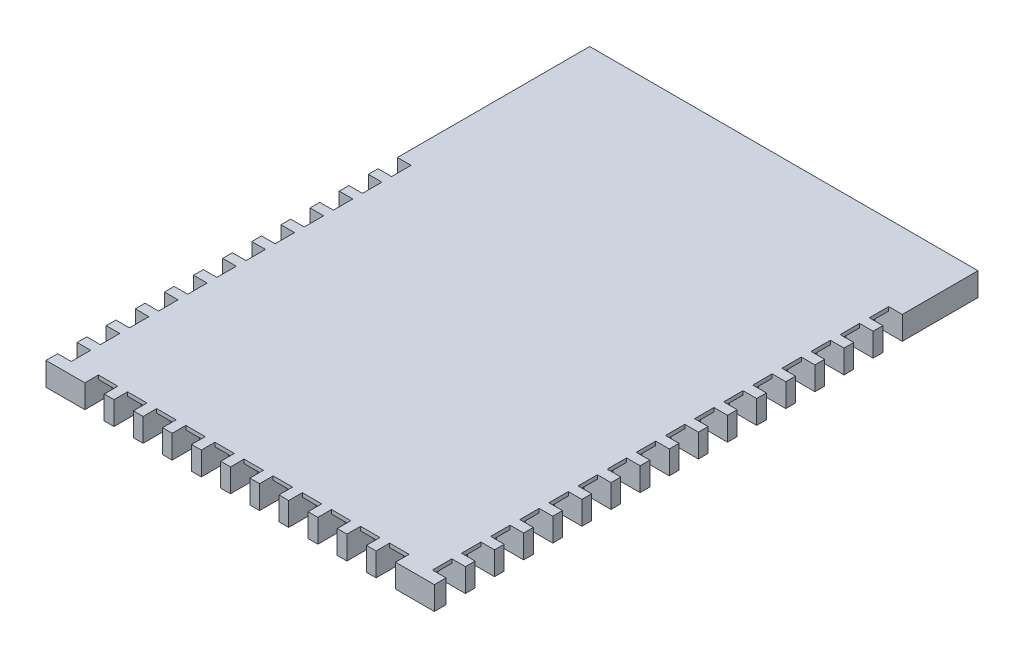
SolidWorks part; units mm, degrees
ref_plane "Front Plane" through (0, 0, 0) normal (0, 0, 1) x (1, 0, 0)
ref_plane "Top Plane" through (0, 0, 0) normal (0, 1, 0) x (1, 0, 0)
ref_plane "Right Plane" through (0, 0, 0) normal (1, 0, 0) x (0, 0, -1)
sketch "Sketch1" plane through (0, 0, 0) normal (0, 1, 0) x (1, 0, 0)
  line L1 (0, 0) -> (10, 0)
  line L2 (0, 0) -> (0, 14)
  line L3 (0, 14) -> (10, 14)
  line L4 (10, 0) -> (10, 14)
extrude "Boss-Extrude1" add sketch "Sketch1" along normal blind 0.6
sketch "Sketch2" plane through (10, 0, 0) normal (1, 0, 0) x (0, 0, -1)
  line L0 (0, 0) -> (14, 0) construction
  line L1 (0.3, 0) -> (0.8, 0)
  line L2 (0.3, 0) -> (0.3, 0.6)
  line L3 (0.3, 0.6) -> (0.8, 0.6)
  line L4 (0.8, 0) -> (0.8, 0.6)
  line L5 (0, 0.6) -> (14, 0.6) construction
  line L6 (1.05, 0) -> (1.05, 0.6)
  line L7 (1.05, 0) -> (1.55, 0)
  line L8 (1.55, 0) -> (1.55, 0.6)
  line L9 (1.05, 0.6) -> (1.55, 0.6)
  line L10 (1.8, 0) -> (1.8, 0.6)
  line L11 (1.8, 0) -> (2.3, 0)
  line L12 (2.3, 0) -> (2.3, 0.6)
  line L13 (1.8, 0.6) -> (2.3, 0.6)
  line L14 (2.55, 0) -> (2.55, 0.6)
  line L15 (2.55, 0) -> (3.05, 0)
  line L16 (3.05, 0) -> (3.05, 0.6)
  line L17 (2.55, 0.6) -> (3.05, 0.6)
  line L18 (3.3, 0) -> (3.3, 0.6)
  line L19 (3.3, 0) -> (3.8, 0)
  line L20 (3.8, 0) -> (3.8, 0.6)
  line L21 (3.3, 0.6) -> (3.8, 0.6)
  line L22 (4.05, 0) -> (4.05, 0.6)
  line L23 (4.05, 0) -> (4.55, 0)
  line L24 (4.55, 0) -> (4.55, 0.6)
  line L25 (4.05, 0.6) -> (4.55, 0.6)
  line L26 (4.8, 0) -> (4.8, 0.6)
  line L27 (4.8, 0) -> (5.3, 0)
  line L28 (5.3, 0) -> (5.3, 0.6)
  line L29 (4.8, 0.6) -> (5.3, 0.6)
  line L30 (5.55, 0) -> (5.55, 0.6)
  line L31 (5.55, 0) -> (6.05, 0)
  line L32 (6.05, 0) -> (6.05, 0.6)
  line L33 (5.55, 0.6) -> (6.05, 0.6)
  line L34 (6.3, 0) -> (6.3, 0.6)
  line L35 (6.3, 0) -> (6.8, 0)
  line L36 (6.8, 0) -> (6.8, 0.6)
  line L37 (6.3, 0.6) -> (6.8, 0.6)
  line L38 (7.05, 0) -> (7.05, 0.6)
  line L39 (7.05, 0) -> (7.55, 0)
  line L40 (7.55, 0) -> (7.55, 0.6)
  line L41 (7.05, 0.6) -> (7.55, 0.6)
  line L42 (7.8, 0) -> (7.8, 0.6)
  line L43 (7.8, 0) -> (8.3, 0)
  line L44 (8.3, 0) -> (8.3, 0.6)
  line L45 (7.8, 0.6) -> (8.3, 0.6)
  line L46 (8.55, 0) -> (8.55, 0.6)
  line L47 (8.55, 0) -> (9.05, 0)
  line L48 (9.05, 0) -> (9.05, 0.6)
  line L49 (8.55, 0.6) -> (9.05, 0.6)
  line L50 (9.3, 0) -> (9.3, 0.6)
  line L51 (9.3, 0) -> (9.8, 0)
  line L52 (9.8, 0) -> (9.8, 0.6)
  line L53 (9.3, 0.6) -> (9.8, 0.6)
  line L54 (10.05, 0) -> (10.05, 0.6)
  line L55 (10.05, 0) -> (10.55, 0)
  line L56 (10.55, 0) -> (10.55, 0.6)
  line L57 (10.05, 0.6) -> (10.55, 0.6)
  line L58 (10.8, 0) -> (10.8, 0.6)
  line L59 (10.8, 0) -> (11.3, 0)
  line L60 (11.3, 0) -> (11.3, 0.6)
  line L61 (10.8, 0.6) -> (11.3, 0.6)
  line L62 (11.55, 0) -> (11.55, 0.6)
  line L63 (11.55, 0) -> (12.05, 0)
  line L64 (12.05, 0) -> (12.05, 0.6)
  line L65 (11.55, 0.6) -> (12.05, 0.6)
  dimension "D1" = 16
extrude "Cut-Extrude1" cut sketch "Sketch2" against normal blind 0.7
sketch "Sketch3" plane through (0, 0, 0) normal (-1, 0, 0) x (0, 0, 1)
  line L0 (-14, 0) -> (0, 0) construction
  line L1 (-0.3, 0) -> (-0.8, 0)
  line L2 (-0.3, 0) -> (-0.3, 0.6)
  line L3 (-0.3, 0.6) -> (-0.8, 0.6)
  line L4 (-0.8, 0) -> (-0.8, 0.6)
  line L5 (-14, 0.6) -> (0, 0.6) construction
  line L6 (-1.05, 0) -> (-1.05, 0.6)
  line L7 (-1.05, 0) -> (-1.55, 0)
  line L8 (-1.55, 0) -> (-1.55, 0.6)
  line L9 (-1.05, 0.6) -> (-1.55, 0.6)
  line L10 (-1.8, 0) -> (-1.8, 0.6)
  line L11 (-1.8, 0) -> (-2.3, 0)
  line L12 (-2.3, 0) -> (-2.3, 0.6)
  line L13 (-1.8, 0.6) -> (-2.3, 0.6)
  line L14 (-2.55, 0) -> (-2.55, 0.6)
  line L15 (-2.55, 0) -> (-3.05, 0)
  line L16 (-3.05, 0) -> (-3.05, 0.6)
  line L17 (-2.55, 0.6) -> (-3.05, 0.6)
  line L18 (-3.3, 0) -> (-3.3, 0.6)
  line L19 (-3.3, 0) -> (-3.8, 0)
  line L20 (-3.8, 0) -> (-3.8, 0.6)
  line L21 (-3.3, 0.6) -> (-3.8, 0.6)
  line L22 (-4.05, 0) -> (-4.05, 0.6)
  line L23 (-4.05, 0) -> (-4.55, 0)
  line L24 (-4.55, 0) -> (-4.55, 0.6)
  line L25 (-4.05, 0.6) -> (-4.55, 0.6)
  line L26 (-4.8, 0) -> (-4.8, 0.6)
  line L27 (-4.8, 0) -> (-5.3, 0)
  line L28 (-5.3, 0) -> (-5.3, 0.6)
  line L29 (-4.8, 0.6) -> (-5.3, 0.6)
  line L30 (-5.55, 0) -> (-5.55, 0.6)
  line L31 (-5.55, 0) -> (-6.05, 0)
  line L32 (-6.05, 0) -> (-6.05, 0.6)
  line L33 (-5.55, 0.6) -> (-6.05, 0.6)
  line L34 (-6.3, 0) -> (-6.3, 0.6)
  line L35 (-6.3, 0) -> (-6.8, 0)
  line L36 (-6.8, 0) -> (-6.8, 0.6)
  line L37 (-6.3, 0.6) -> (-6.8, 0.6)
  line L38 (-7.05, 0) -> (-7.05, 0.6)
  line L39 (-7.05, 0) -> (-7.55, 0)
  line L40 (-7.55, 0) -> (-7.55, 0.6)
  line L41 (-7.05, 0.6) -> (-7.55, 0.6)
  line L42 (-7.8, 0) -> (-7.8, 0.6)
  line L43 (-7.8, 0) -> (-8.3, 0)
  line L44 (-8.3, 0) -> (-8.3, 0.6)
  line L45 (-7.8, 0.6) -> (-8.3, 0.6)
  line L46 (-8.55, 0) -> (-8.55, 0.6)
  line L47 (-8.55, 0) -> (-9.05, 0)
  line L48 (-9.05, 0) -> (-9.05, 0.6)
  line L49 (-8.55, 0.6) -> (-9.05, 0.6)
  dimension "D1" = 12
extrude "Cut-Extrude2" cut sketch "Sketch3" against normal blind 0.7
sketch "Sketch4" plane through (0, 0, 0) normal (0, 0, 1) x (1, 0, 0)
  line L0 (0, 0) -> (10, 0) construction
  line L1 (1, 0) -> (1.5, 0)
  line L2 (1, 0) -> (1, 0.6)
  line L3 (1, 0.6) -> (1.5, 0.6)
  line L4 (1.5, 0) -> (1.5, 0.6)
  line L5 (0, 0.6) -> (10, 0.6) construction
  line L6 (1.75, 0) -> (1.75, 0.6)
  line L7 (1.75, 0) -> (2.25, 0)
  line L8 (2.25, 0) -> (2.25, 0.6)
  line L9 (1.75, 0.6) -> (2.25, 0.6)
  line L10 (2.5, 0) -> (2.5, 0.6)
  line L11 (2.5, 0) -> (3, 0)
  line L12 (3, 0) -> (3, 0.6)
  line L13 (2.5, 0.6) -> (3, 0.6)
  line L14 (3.25, 0) -> (3.25, 0.6)
  line L15 (3.25, 0) -> (3.75, 0)
  line L16 (3.75, 0) -> (3.75, 0.6)
  line L17 (3.25, 0.6) -> (3.75, 0.6)
  line L18 (4, 0) -> (4, 0.6)
  line L19 (4, 0) -> (4.5, 0)
  line L20 (4.5, 0) -> (4.5, 0.6)
  line L21 (4, 0.6) -> (4.5, 0.6)
  line L22 (4.75, 0) -> (4.75, 0.6)
  line L23 (4.75, 0) -> (5.25, 0)
  line L24 (5.25, 0) -> (5.25, 0.6)
  line L25 (4.75, 0.6) -> (5.25, 0.6)
  line L26 (5.5, 0) -> (5.5, 0.6)
  line L27 (5.5, 0) -> (6, 0)
  line L28 (6, 0) -> (6, 0.6)
  line L29 (5.5, 0.6) -> (6, 0.6)
  line L30 (6.25, 0) -> (6.25, 0.6)
  line L31 (6.25, 0) -> (6.75, 0)
  line L32 (6.75, 0) -> (6.75, 0.6)
  line L33 (6.25, 0.6) -> (6.75, 0.6)
  line L34 (7, 0) -> (7, 0.6)
  line L35 (7, 0) -> (7.5, 0)
  line L36 (7.5, 0) -> (7.5, 0.6)
  line L37 (7, 0.6) -> (7.5, 0.6)
  line L38 (7.75, 0) -> (7.75, 0.6)
  line L39 (7.75, 0) -> (8.25, 0)
  line L40 (8.25, 0) -> (8.25, 0.6)
  line L41 (7.75, 0.6) -> (8.25, 0.6)
  line L42 (8.5, 0) -> (8.5, 0.6)
  line L43 (8.5, 0) -> (9, 0)
  line L44 (9, 0) -> (9, 0.6)
  line L45 (8.5, 0.6) -> (9, 0.6)
  dimension "D1" = 11
extrude "Cut-Extrude3" cut sketch "Sketch4" against normal blind 0.7
sketch "Sketch6" plane through (0.7, 0, 0) normal (-1, 0, 0) x (0, 0, 1)
  line L0 (-0.3, 0) -> (-0.3, 0.6) construction
  line L1 (-9.05, 0.6) -> (-0.3, 0.6)
  line L2 (-9.05, 0.6) -> (-9.05, 0.5)
  line L3 (-9.05, 0.5) -> (-0.3, 0.5)
  line L4 (-0.3, 0.6) -> (-0.3, 0.5)
extrude "Boss-Extrude2" add sketch "Sketch6" along normal blind 0.35
sketch "Sketch7" plane through (9.3, 0, 0) normal (1, 0, 0) x (0, 0, -1)
  line L0 (12.05, 0) -> (12.05, 0.6) construction
  line L1 (0.3, 0.6) -> (12.05, 0.6)
  line L2 (0.3, 0.6) -> (0.3, 0.5)
  line L3 (0.3, 0.5) -> (12.05, 0.5)
  line L4 (12.05, 0.6) -> (12.05, 0.5)
extrude "Boss-Extrude3" add sketch "Sketch7" along normal blind 0.35
sketch "Sketch8" plane through (0, 0, -0.7) normal (0, 0, 1) x (1, 0, 0)
  line L0 (9, 0) -> (9, 0.6) construction
  line L1 (1, 0.6) -> (9, 0.6)
  line L2 (1, 0.6) -> (1, 0.5)
  line L3 (1, 0.5) -> (9, 0.5)
  line L4 (9, 0.6) -> (9, 0.5)
extrude "Boss-Extrude4" add sketch "Sketch8" along normal blind 0.35
